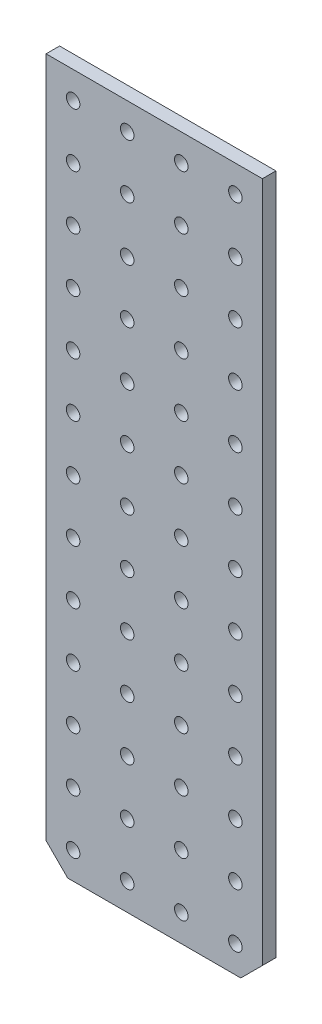
SolidWorks part; units mm, degrees
ref_plane "Front Plane" through (0, 0, 0) normal (0, 0, 1) x (1, 0, 0)
ref_plane "Top Plane" through (0, 0, 0) normal (0, 1, 0) x (1, 0, 0)
ref_plane "Right Plane" through (0, 0, 0) normal (1, 0, 0) x (0, 0, -1)
sketch "Sketch1" plane through (0, 0, 0) normal (0, 0, 1) x (1, 0, 0)
  line L1 (-25.4, -82.55) -> (25.4, -82.55)
  line L2 (-25.4, -82.55) -> (-25.4, 82.55)
  line L3 (-25.4, 82.55) -> (25.4, 82.55)
  line L4 (25.4, -82.55) -> (25.4, 82.55)
  line L5 (-25.4, -82.55) -> (25.4, 82.55) construction
  line L6 (-25.4, 82.55) -> (25.4, -82.55) construction
  point P0 (0, 0)
  dimension "D1" = 165.1
  dimension "D2" = 50.8
extrude "Boss-Extrude1" add sketch "Sketch1" along normal blind 3.175
sketch "Sketch2" plane through (0, 0, 3.175) normal (0, 0, 1) x (1, 0, 0)
  line L0 (0, 82.55) -> (0, -82.55) construction
  line L1 (25.4, 82.55) -> (-25.4, 82.55) construction
  line L2 (-25.4, -82.55) -> (25.4, -82.55) construction
  circle A0 centre (-6.35, -76.2) radius 1.5875
  dimension "D1" = 3.175
  dimension "D2" = 12.7
  dimension "D3" = 6.35
extrude "Cut-Extrude1" cut sketch "Sketch2" against normal through all
pattern_linear "LPattern1" count 3 spacing 12.7 along (1, 0, 0) count 2 spacing 12.7 along (-1, 0, 0) of "Cut-Extrude1"
pattern_linear "LPattern2" count 13 spacing 12.7 along (0, 1, 0) of "LPattern1", "Cut-Extrude1"
chamfer "Chamfer1" distance 5.08 angle 45 2 edges at (-25.4, -82.55, 1.5875) (25.4, -82.55, 1.5875)
